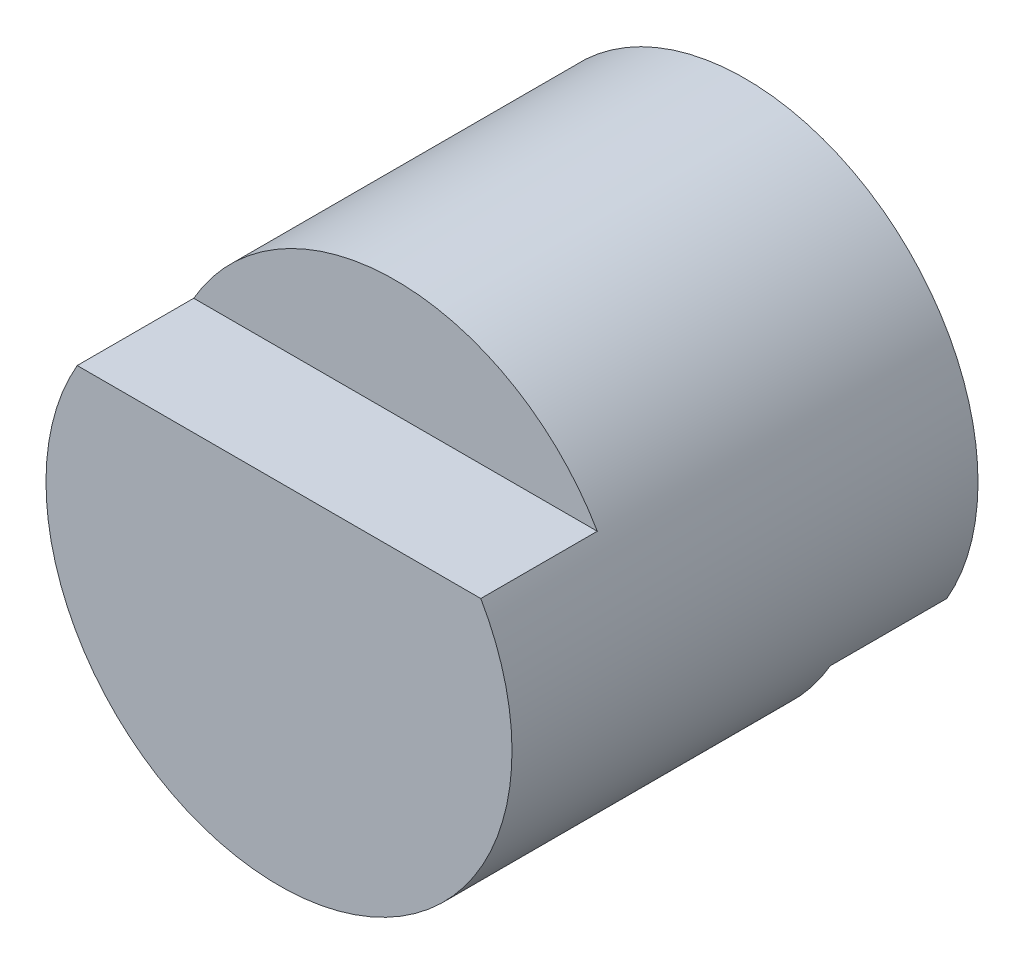
SolidWorks part; units mm, degrees
ref_plane "Front" through (0, 0, 0) normal (0, 0, 1) x (1, 0, 0)
ref_plane "Top" through (0, 0, 0) normal (0, 1, 0) x (1, 0, 0)
ref_plane "Right" through (0, 0, 0) normal (1, 0, 0) x (0, 0, -1)
sketch "Sketch1" plane through (0, 0, 0) normal (0, 0, 1) x (1, 0, 0)
  circle A0 centre (0, 0) radius 2
  dimension "D1" = 4
extrude "Boss-Extrude1" add sketch "Sketch1" along normal blind 4
sketch "Sketch2" plane through (0, 0, 4) normal (0, 0, 1) x (1, 0, 0)
  line L0 (-1.7321, 1) -> (1.7321, 1)
  circle A0 centre (0, 0) radius 2 construction
  arc A1 (-1.7321, 1) -> (1.7321, 1) centre (0, 0) cw
  dimension "D1" = 1
extrude "Cut-Extrude2" cut sketch "Sketch2" against normal blind 1
sketch "Sketch4" plane through (0, 0, 0) normal (0, 0, -1) x (-1, 0, 0)
  line L0 (-1.7321, -1) -> (1.7321, -1)
  circle A0 centre (0, 0) radius 2 construction
  arc A1 (-1.7321, -1) -> (1.7321, -1) centre (0, 0) ccw
  dimension "D1" = 1
extrude "Cut-Extrude3" cut sketch "Sketch4" against normal blind 1
